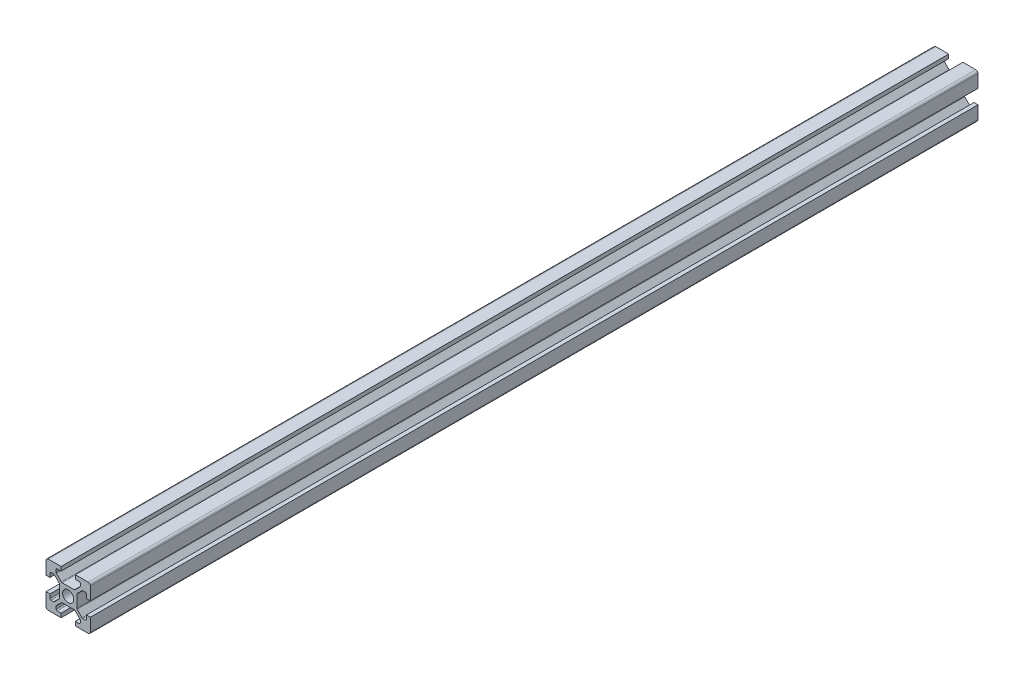
SolidWorks part; units mm, degrees
material "1060 Alloy"
ref_plane "Front Plane" through (0, 0, 0) normal (0, 0, 1) x (1, 0, 0)
ref_plane "Top Plane" through (0, 0, 0) normal (0, 1, 0) x (1, 0, 0)
ref_plane "Right Plane" through (0, 0, 0) normal (1, 0, 0) x (0, 0, -1)
sketch "Sketch1" plane through (0, 0, 0) normal (0, 0, 1) x (1, 0, 0)
  line L0 (20, 0) -> (-8.059, 28.059) construction
  line L1 (0, 0) -> (6.8, 0)
  line L2 (0, 0) -> (0, 6.8)
  line L3 (0, 20) -> (6.8, 20)
  line L4 (20, 0) -> (20, 6.8)
  line L5 (6.8, 20) -> (6.8, 18.2)
  line L6 (20, 20) -> (8.2322, 8.2322) construction
  line L7 (12.95, 6.1) -> (7.05, 6.1)
  line L8 (13.9, 7.05) -> (13.9, 12.95)
  line L9 (12.95, 13.9) -> (7.05, 13.9)
  line L10 (6.1, 7.05) -> (6.1, 12.95)
  line L11 (13.9, 6.1) -> (6.1, 13.9) construction
  line L12 (13.9, 13.9) -> (6.1, 6.1) construction
  line L13 (4.55, 16.4) -> (7.05, 13.9)
  line L14 (13.2, 18.2) -> (13.2, 20)
  line L15 (1.8, 6.8) -> (0, 6.8)
  line L16 (0, 13.2) -> (0, 20)
  line L17 (0, 13.2) -> (1.8, 13.2)
  line L18 (10, 10) -> (10, 13.9) construction
  line L19 (16.4, 4.55) -> (13.9, 7.05)
  line L20 (4.55, 16.4) -> (4.55, 18.2)
  line L21 (4.55, 18.2) -> (6.8, 18.2)
  line L22 (13.2, 18.2) -> (15.45, 18.2)
  line L23 (15.45, 18.2) -> (15.45, 16.4)
  line L24 (15.45, 16.4) -> (12.95, 13.9)
  line L25 (16.4, 4.55) -> (18.2, 4.55)
  line L26 (18.2, 4.55) -> (18.2, 6.8)
  line L27 (20, 6.8) -> (18.2, 6.8)
  line L28 (18.2, 13.2) -> (20, 13.2)
  line L29 (18.2, 13.2) -> (18.2, 15.45)
  line L30 (18.2, 15.45) -> (16.4, 15.45)
  line L31 (16.4, 15.45) -> (13.9, 12.95)
  line L32 (1.8, 4.55) -> (3.6, 4.55)
  line L33 (3.6, 15.45) -> (6.1, 12.95)
  line L34 (3.6, 15.45) -> (1.8, 15.45)
  line L35 (1.8, 15.45) -> (1.8, 13.2)
  line L38 (3.6, 4.55) -> (6.1, 7.05)
  line L39 (1.8, 6.8) -> (1.8, 4.55)
  line L40 (15.45, 3.6) -> (12.95, 6.1)
  line L41 (4.55, 3.6) -> (7.05, 6.1)
  line L42 (4.55, 1.8) -> (4.55, 3.6)
  line L43 (6.8, 1.8) -> (4.55, 1.8)
  line L44 (6.8, 1.8) -> (6.8, 0)
  line L45 (15.45, 3.6) -> (15.45, 1.8)
  line L46 (15.45, 1.8) -> (13.2, 1.8)
  line L47 (13.2, 0) -> (13.2, 1.8)
  line L48 (13.2, 20) -> (20, 20)
  line L49 (20, 13.2) -> (20, 20)
  line L50 (13.2, 0) -> (20, 0)
  line L51 (6.1, 6.1) -> (-5.5045, -5.5045) construction
  circle A0 centre (10, 10) radius 2.5
  point P25 (10, 16.4)
  point P39 (13.2, 19.1)
  point P46 (0.9, 6.8)
  dimension "D3" = 5
  dimension "D2" = 20
  dimension "D4" = 7.8
  dimension "D5" = 7.8
  dimension "D6" = 6.8
  dimension "D7" = 6.8
  dimension "D8" = 1.8
  dimension "D9" = 10.9
  dimension "D10" = 1.8
  dimension "D11" = 10.9
  dimension "D12" = 20
extrude "Boss-Extrude1" add sketch "Sketch1" along normal blind 400 contours L47 L50 L4 L27 L26 L25 L19 L8 L31 L30 L29 L28 L49 L48 L14 L22 L23 L24 L9 L13 L20 L21 L5 L3 L16 L17 L35 L34 L33 L10 L38 L32 L39 L15 L2 L1 L44 L43 L42 L41 L7 L40 L45 L46 A0
fillet "Fillet1" radius 1 4 edges at (20, 20, 200) (20, 0, 200) (0, 0, 200) (0, 20, 200)
fillet "Fillet2" radius 0.5 6 edges at (4.55, 18.2, 200) (4.55, 16.4, 200) (7.05, 13.9, 200) (15.45, 18.2, 200) (15.45, 16.4, 200) (12.95, 13.9, 200)
fillet "Fillet3" radius 0.5 6 edges at (18.2, 15.45, 200) (16.4, 15.45, 200) (13.9, 12.95, 200) (18.2, 4.55, 200) (13.9, 7.05, 200) (16.4, 4.55, 200)
fillet "Fillet4" radius 0.5 6 edges at (1.8, 15.45, 200) (3.6, 15.45, 200) (6.1, 12.95, 200) (3.6, 4.55, 200) (1.8, 4.55, 200) (6.1, 7.05, 200)
fillet "Fillet5" radius 0.5 6 edges at (7.05, 6.1, 200) (4.55, 3.6, 200) (4.55, 1.8, 200) (15.45, 1.8, 200) (15.45, 3.6, 200) (12.95, 6.1, 200)
